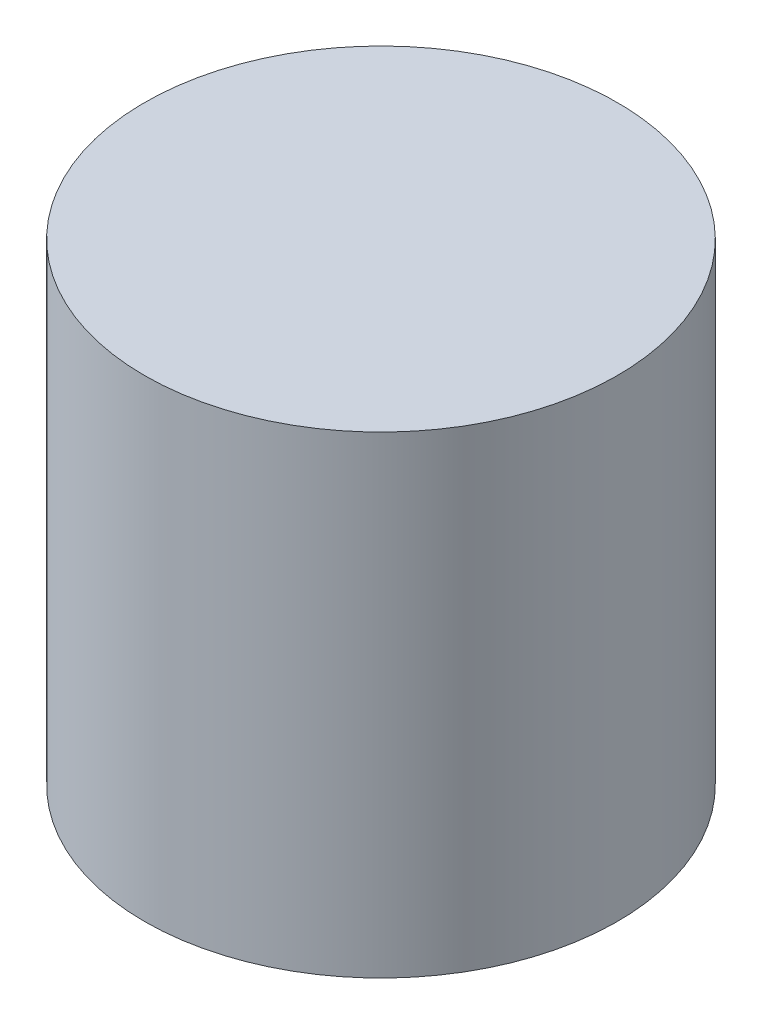
SolidWorks part; units mm, degrees
ref_plane "Front Plane" through (0, 0, 0) normal (0, 0, 1) x (1, 0, 0)
ref_plane "Top Plane" through (0, 0, 0) normal (0, 1, 0) x (1, 0, 0)
ref_plane "Right Plane" through (0, 0, 0) normal (1, 0, 0) x (0, 0, -1)
sketch "Sketch1" plane through (0, 0, 0) normal (0, 1, 0) x (1, 0, 0)
  circle A0 centre (0, 0) radius 45
extrude "Boss-Extrude1" add sketch "Sketch1" along normal blind 90
sketch "Sketch2" plane through (0, 0, 0) normal (0, 0, 1) x (1, 0, 0)
  line L0 (45, 0) -> (45, 90) construction
  ellipse E0 centre (55, 45) end of major axis (55, 13) minor radius 18
  point P1 (45, 18.3927)
  point P9 (45, 71.6073)
  point P10 (0, 0)
  dimension "D1" = 10
  dimension "D2" = 0
  dimension "D3" = 0
sketch3d "3DSketch1"
sketch "Sketch3" plane through (55, 0, 0) normal (-1, 0, 0) x (0, 0, 1)
  line L0 (0, 13) -> (0, 77) construction
  ellipse E0 centre (0, 71.6073) end of major axis (-8, 71.6073) minor radius 5
  point P1 (0, 0)
equation "\"90.oomm\"=10"
